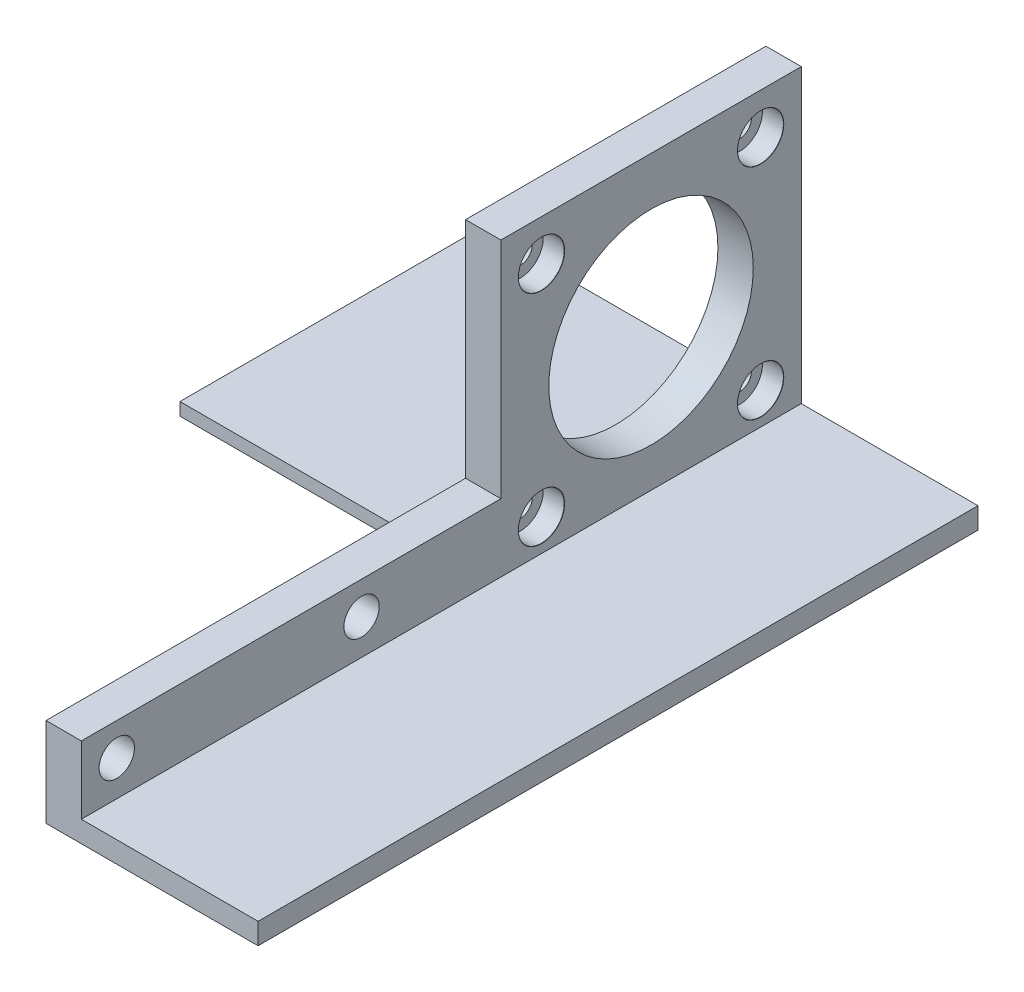
SolidWorks part; units mm, degrees
ref_plane "Front Plane" through (0, 0, 0) normal (0, 0, 1) x (1, 0, 0)
ref_plane "Top Plane" through (0, 0, 0) normal (0, 1, 0) x (1, 0, 0)
ref_plane "Right Plane" through (0, 0, 0) normal (1, 0, 0) x (0, 0, -1)
sketch "Sketch1" plane through (0, 0, 0) normal (1, 0, 0) x (0, 0, -1)
  line L0 (-45.5856, 0) -> (56.25, 0) construction
  line L1 (-45.5856, 0) -> (56.25, 0)
  line L2 (-45.5856, 0) -> (-45.5856, -3)
  line L3 (-45.5856, -3) -> (56.25, -3)
  line L4 (56.25, 0) -> (56.25, -3)
  arc A0 (56.25, 0) -> (61.25, 5) centre (56.25, 5) ccw construction
  point P6 (56.25, 0)
  point P10 (-45.3243, 0)
  point P11 (-41.2223, 0)
  dimension "D1" = 3
extrude "Boss-Extrude1" add sketch "Sketch1" along a picked direction on the side of the normal mid plane 25 contours L3 L4 L1 L2
sketch "Sketch2" plane through (-12.5, 0, 0) normal (-1, 0, 0) x (0, 0, 1)
  line L1 (-56.25, -3) -> (-13.7634, -3)
  line L2 (-56.25, -3) -> (-56.25, -1.2)
  line L3 (-56.25, -1.2) -> (-13.7634, -1.2)
  line L4 (-13.7634, -3) -> (-13.7634, -1.2)
  line L5 (-13.7634, 32.2769) -> (-13.7634, 7.4259) construction
  line L8 (-48.8976, -1.2) -> (-21.1024, -1.2) construction
extrude "Boss-Extrude2" add sketch "Sketch2" along normal up to surface (45.4 mm away)
sketch "Sketch3" plane through (-12.5, 0, 0) normal (-1, 0, 0) x (0, 0, 1)
  line L0 (-13.7634, -1.2) -> (-13.7634, -3) construction
  line L1 (-56.25, -1.2) -> (-13.7634, -1.2)
  line L2 (-56.25, -1.2) -> (-56.25, 41.2866)
  line L3 (-56.25, 41.2866) -> (-13.7634, 41.2866)
  line L4 (-13.7634, -1.2) -> (-13.7634, 41.2866)
  line L5 (-13.7634, -3) -> (-13.7634, -1.2) construction
  point P5 (-13.7634, -1.2)
extrude "Boss-Extrude3" add sketch "Sketch3" along normal up to surface (5 mm away)
sketch "Sketch4" plane through (-12.5, 0, 0) normal (1, 0, 0) x (0, 0, -1)
  circle A0 centre (19.5, 4.5) radius 1.5541 construction
  circle A1 centre (50.5, 4.5) radius 1.5541 construction
  circle A2 centre (50.5, 35.5) radius 1.5541 construction
  circle A3 centre (19.5, 35.5) radius 1.5541 construction
  circle A4 centre (19.5, 4.5) radius 1.5541
  circle A5 centre (50.5, 4.5) radius 1.5541
  circle A6 centre (50.5, 35.5) radius 1.5541
  circle A7 centre (19.5, 35.5) radius 1.5541
  point P0 (19.5, 4.5)
  point P2 (50.5, 4.5)
  point P4 (50.5, 35.5)
  point P6 (19.5, 35.5)
hole_wizard "CBORE for M3 SHCS2" positions "Sketch4" profile "Sketch8" counterbore size "M3" standard "ANSI Metric" end condition through all
sketch "Sketch8" plane through (-12.5, 4.5, -19.5) normal (0, 1, 0) x (0, 0, -1)
  line L0 (0, 0) -> (0, 45.4)
  line L1 (0, 45.4) -> (1.7, 45.4)
  line L3 (1.7, 45.4) -> (1.7, 3)
  line L4 (3.25, 3) -> (1.7, 3)
  line L5 (3.25, 3) -> (3.25, 0.025)
  line L6 (3.25, 0.025) -> (3.275, 0)
  line L7 (3.275, 0) -> (0, 0)
  line L8 (-3.25, 0.025) -> (-3.275, 0) construction
  line L11 (0, -6.35) -> (0, 107.95) construction
  dimension "Thru Hole Dia." = 3.4
  dimension "Thru Hole Depth" = 45.4
  dimension "C'Bore Dia." = 6.5
  dimension "C'Bore Depth" = 3
  dimension "Near C'Sink Dia." = 6.55
  dimension "Near C'Sink Angle" = 90
sketch "Sketch9" plane through (-12.5, 0, 0) normal (1, 0, 0) x (0, 0, -1)
  circle A0 centre (35, 20) radius 13.462 construction
  circle A1 centre (35, 20) radius 13.462 construction
  circle A2 centre (35, 20) radius 14.462
  dimension "D1" = 1
extrude "Cut-Extrude1" cut sketch "Sketch9" against normal blind 10
sketch "Sketch10" plane through (-12.5, 0, 0) normal (-1, 0, 0) x (0, 0, 1)
  line L0 (-45.3866, 9.6) -> (-4.2134, 9.6) construction
  line L1 (45.5856, -3) -> (-13.7634, -3)
  line L2 (45.5856, -3) -> (45.5856, 9.6)
  line L3 (45.5856, 9.6) -> (-13.7634, 9.6)
  line L4 (-13.7634, -3) -> (-13.7634, 9.6)
  point P5 (-11.9907, 11.2332)
extrude "Boss-Extrude4" add sketch "Sketch10" along normal up to surface (5 mm away) up to face at (-17.5, 20, -49.462)
sketch "Sketch11" plane through (-17.5, 0, 0) normal (-1, 0, 0) x (0, 0, 1)
  circle A0 centre (5.95, 5) radius 2.5 construction
  circle A1 centre (40.5742, 5) radius 2.5 construction
  circle A2 centre (5.95, 5) radius 2.5
  circle A3 centre (40.5742, 5) radius 2.5
extrude "Cut-Extrude2" cut sketch "Sketch11" against normal blind 10
